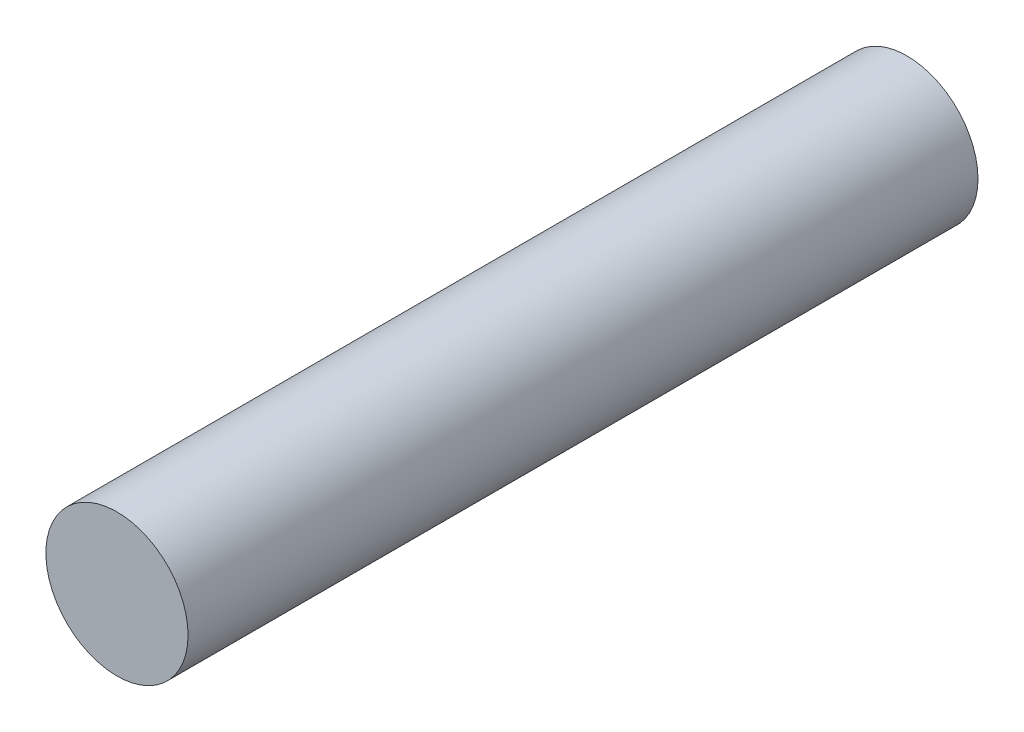
SolidWorks part; units mm, degrees
ref_plane "Plan de face" through (0, 0, 0) normal (0, 0, 1) x (1, 0, 0)
ref_plane "Plan de dessus" through (0, 0, 0) normal (0, 1, 0) x (1, 0, 0)
ref_plane "Plan de droite" through (0, 0, 0) normal (1, 0, 0) x (0, 0, -1)
sketch "Esquisse1" plane through (0, 0, 0) normal (0, 0, 1) x (1, 0, 0)
  circle A1 centre (-2.1392, 7.0584) radius 1.8
extrude "Boss.-Extru.2" add sketch "Esquisse1" along normal blind 20
